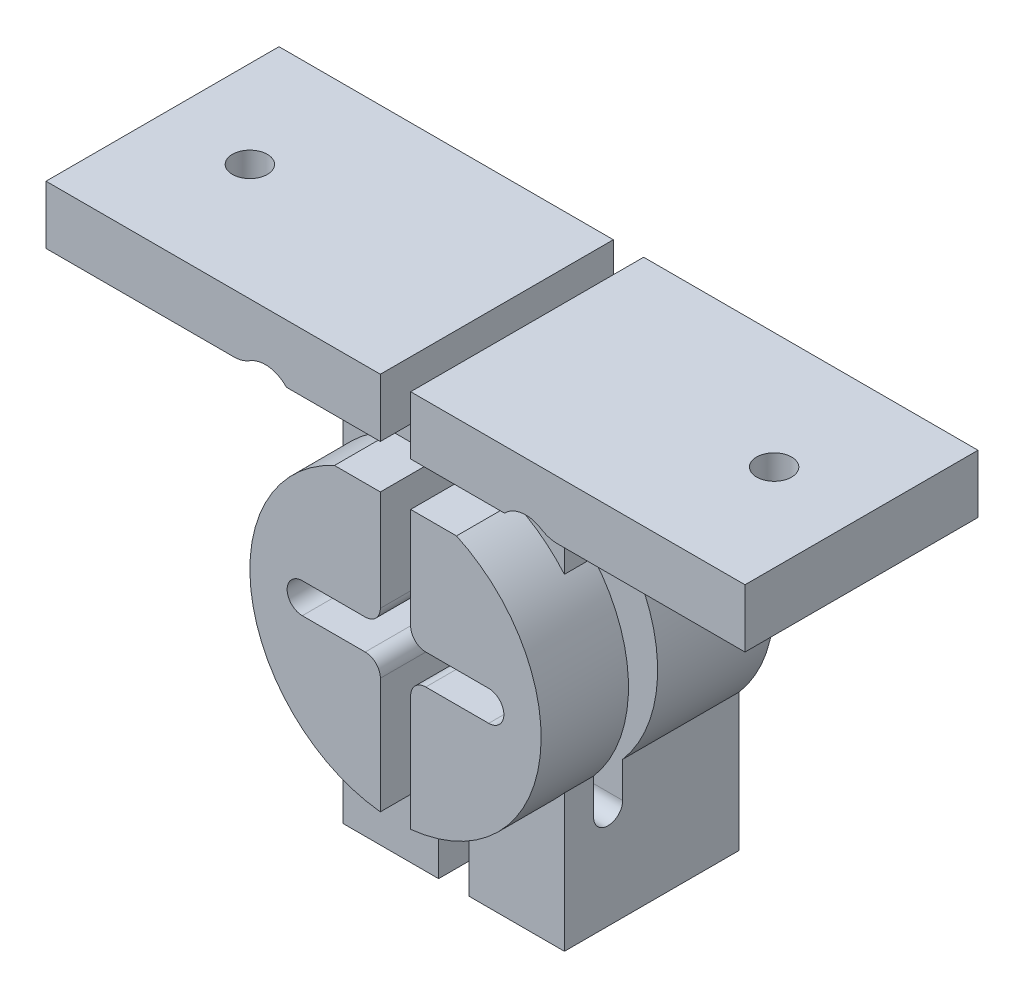
SolidWorks part; units mm, degrees
ref_plane "Front Plane" through (0, 0, 0) normal (0, 0, 1) x (1, 0, 0)
ref_plane "Top Plane" through (0, 0, 0) normal (0, 1, 0) x (1, 0, 0)
ref_plane "Right Plane" through (0, 0, 0) normal (1, 0, 0) x (0, 0, -1)
sketch "Sketch1" plane through (0, 0, 0) normal (0, 0, 1) x (1, 0, 0)
  line L1 (38.1, -25.4) -> (-38.1, -25.4)
  line L2 (38.1, -25.4) -> (38.1, 25.4)
  line L3 (38.1, 25.4) -> (-38.1, 25.4)
  line L4 (-38.1, -25.4) -> (-38.1, 25.4)
  line L5 (38.1, -25.4) -> (-38.1, 25.4) construction
  line L6 (38.1, 25.4) -> (-38.1, -25.4) construction
  point P0 (0, 0)
  dimension "D1" = 76.2
  dimension "D2" = 50.8
extrude "Boss-Extrude1" add sketch "Sketch1" along normal blind 25.4
sketch "Sketch2" plane through (0, 0, 25.4) normal (0, 0, 1) x (1, 0, 0)
  line L0 (0, 15.748) -> (0, 25.4) construction
  line L1 (38.1, 25.4) -> (-38.1, 25.4) construction
  line L2 (-38.1, 25.4) -> (-38.1, -25.4) construction
  line L3 (38.1, -25.4) -> (-38.1, -25.4)
  line L4 (38.1, -25.4) -> (38.1, 19.05)
  line L5 (38.1, 19.05) -> (-38.1, 19.05)
  line L6 (-38.1, -25.4) -> (-38.1, 19.05)
  line L7 (38.1, -25.4) -> (-38.1, 19.05) construction
  line L8 (38.1, 19.05) -> (-38.1, -25.4) construction
  line L9 (38.1, -25.4) -> (38.1, 25.4) construction
  line L10 (-38.1, -25.4) -> (38.1, -25.4) construction
  circle A0 centre (0, -0.127) radius 15.875
  point P7 (0, -3.175)
  dimension "D1" = 31.75
  dimension "D2" = 6.35
  dimension "D3" = 3.302
extrude "Cut-Extrude1" cut sketch "Sketch2" against normal blind 6.35
sketch "Sketch3" plane through (0, 0, 25.4) normal (0, 0, 1) x (1, 0, 0)
  line L0 (38.1, 25.4) -> (-38.1, 25.4) construction
  line L1 (10.16, -1.651) -> (3.302, -1.651)
  line L2 (-1.651, 3.302) -> (-1.651, 25.4)
  line L3 (10.16, 1.651) -> (3.302, 1.651)
  line L4 (-3.302, -1.651) -> (-10.16, -1.651)
  line L5 (-3.302, 1.651) -> (-10.16, 1.651)
  line L7 (1.651, -25.4) -> (-1.651, -25.4)
  line L8 (1.651, -25.4) -> (1.651, -3.302)
  line L9 (1.651, 25.4) -> (-1.651, 25.4)
  line L10 (-1.651, -25.4) -> (-1.651, -3.302)
  line L16 (1.651, 3.302) -> (1.651, 25.4)
  arc A0 (-10.16, 1.651) -> (-10.16, -1.651) centre (-10.16, 0) ccw
  arc A1 (10.16, -1.651) -> (10.16, 1.651) centre (10.16, 0) ccw
  arc A2 (1.651, 3.302) -> (3.302, 1.651) centre (3.302, 3.302) ccw
  arc A3 (1.651, -3.302) -> (3.302, -1.651) centre (3.302, -3.302) cw
  arc A4 (-1.651, -3.302) -> (-3.302, -1.651) centre (-3.302, -3.302) ccw
  arc A5 (-1.651, 3.302) -> (-3.302, 1.651) centre (-3.302, 3.302) cw
  point P0 (0, 0)
  point P6 (0, 0)
  point P25 (-1.651, -1.651)
  point P28 (-1.651, 1.651)
  dimension "D1" = 1.651
  dimension "D2" = 3.302
extrude "Cut-Extrude2" cut sketch "Sketch3" against normal blind 12.7
sketch "Sketch4" plane through (0, 0, 19.05) normal (0, 0, 1) x (1, 0, 0)
  line L1 (0, 25.8695) -> (0, -26.1235) construction
  line L2 (1.651, -25.4) -> (38.1, -25.4) construction
  line L3 (12.065, -25.4) -> (38.1, -25.4)
  line L4 (12.065, -25.4) -> (12.065, -10.4445)
  line L5 (12.065, 19.05) -> (38.1, 19.05)
  line L6 (38.1, -25.4) -> (38.1, 19.05)
  line L9 (12.065, -25.4) -> (38.1, 19.05) construction
  line L11 (12.065, 19.05) -> (38.1, -25.4) construction
  line L12 (1.651, -25.4) -> (1.651, -15.9159) construction
  line L13 (12.065, 10.1905) -> (12.065, 19.05)
  line L14 (-12.065, 19.05) -> (-38.1, -25.4) construction
  line L15 (-12.065, -25.4) -> (-38.1, 19.05) construction
  line L16 (-12.065, 10.1905) -> (-12.065, 19.05)
  line L17 (-38.1, -25.4) -> (-38.1, 19.05)
  line L18 (-12.065, 19.05) -> (-38.1, 19.05)
  line L20 (-12.065, -25.4) -> (-12.065, -10.4445)
  line L21 (-12.065, -25.4) -> (-38.1, -25.4)
  arc A0 (12.065, -10.4445) -> (12.065, 10.1905) centre (0, -0.127) ccw
  arc A3 (-12.065, -10.4445) -> (-12.065, 10.1905) centre (0, -0.127) cw
  arc A4 (1.651, -15.9159) -> (1.651, 15.6619) centre (0, -0.127) ccw construction
  point P2 (25.0825, -3.175)
  point P21 (-25.0825, -3.175)
  dimension "D1" = 10.414
  dimension "D2" = 12.065
  dimension "D3" = 14.9555
  dimension "D4" = 44.45
  dimension "D5" = 8.8595
  dimension "D6" = 26.035
extrude "Cut-Extrude3" cut sketch "Sketch4" against normal up to vertex
sketch "Sketch6" plane through (0, 0, 0) normal (1, 0, 0) x (0, 0, -1)
  line L2 (-12.7, -14.3284) -> (-12.7, 14.0744)
  line L4 (-15.875, -14.3284) -> (-15.875, 14.0744)
  line L7 (-12.7, -25.4) -> (-12.7, -3.302) construction
  arc A0 (-12.7, 14.0744) -> (-15.875, 14.0744) centre (-14.2875, 14.0744) ccw
  arc A1 (-15.875, -14.3284) -> (-12.7, -14.3284) centre (-14.2875, -14.3284) ccw
  point P0 (-14.2875, -0.127)
extrude "Cut-Extrude4" cut sketch "Sketch6" against normal up to vertex and the other way up to vertex
sketch "Sketch7" plane through (0, 0, 19.05) normal (0, 0, 1) x (1, 0, 0)
  line L0 (0, 0) -> (0, 34.1708) construction
  circle A0 centre (14.1939, 16.8687) radius 3.175
  circle A1 centre (-14.1939, 16.8687) radius 3.175
  dimension "D3" = 6.35
  dimension "D1" = 3.048
extrude "Cut-Extrude5" cut sketch "Sketch7" against normal up to vertex and the other way up to vertex
fillet "Fillet1" radius 3.302 6 edges at (-12.065, 14.5132, 6.3809) (-12.065, 14.5132, 17.4316) (-16.501, 19.05, 12.7) (12.065, 14.5132, 6.3809) (12.065, 14.5132, 17.4316) (16.501, 19.05, 12.7)
sketch "Sketch8" plane through (0, 25.4, 0) normal (0, 1, 0) x (1, 0, 0)
  line L0 (-38.1, -12.7) -> (38.1, -12.7) construction
  line L1 (-38.1, -25.4) -> (-38.1, 0) construction
  line L2 (38.1, -25.4) -> (38.1, 0) construction
  circle A0 centre (-28.575, -12.7) radius 1.905
  circle A1 centre (28.575, -12.7) radius 1.905
  dimension "D1" = 3.81
  dimension "D2" = 9.525
  dimension "D3" = 9.525
extrude "Cut-Extrude6" cut sketch "Sketch8" against normal up to vertex
sketch "Sketch9" plane through (0, 0, 12.7) normal (0, 0, 1) x (1, 0, 0)
  line L1 (1.651, -25.4) -> (-1.651, -25.4)
  line L2 (1.651, -25.4) -> (1.651, 25.4)
  line L3 (1.651, 25.4) -> (-1.651, 25.4)
  line L4 (-1.651, -25.4) -> (-1.651, 25.4)
  line L5 (1.651, -25.4) -> (-1.651, 25.4) construction
  line L6 (1.651, 25.4) -> (-1.651, -25.4) construction
  point P0 (0, 0)
extrude "Cut-Extrude7" cut sketch "Sketch9" against normal up to vertex
sketch "Sketch10" plane through (0, 0, 19.05) normal (0, 0, 1) x (1, 0, 0)
  line L1 (11.8868, 14.2875) -> (-11.8868, 14.2875)
  line L2 (11.8868, 14.2875) -> (11.8868, 19.05)
  line L3 (11.8868, 19.05) -> (-11.8868, 19.05)
  line L4 (-11.8868, 14.2875) -> (-11.8868, 19.05)
  line L5 (11.8868, 14.2875) -> (-11.8868, 19.05) construction
  line L6 (11.8868, 19.05) -> (-11.8868, 14.2875) construction
  point P0 (0, 16.6688)
  dimension "D1" = 4.7625
extrude "Cut-Extrude8" cut sketch "Sketch10" along normal up to vertex
